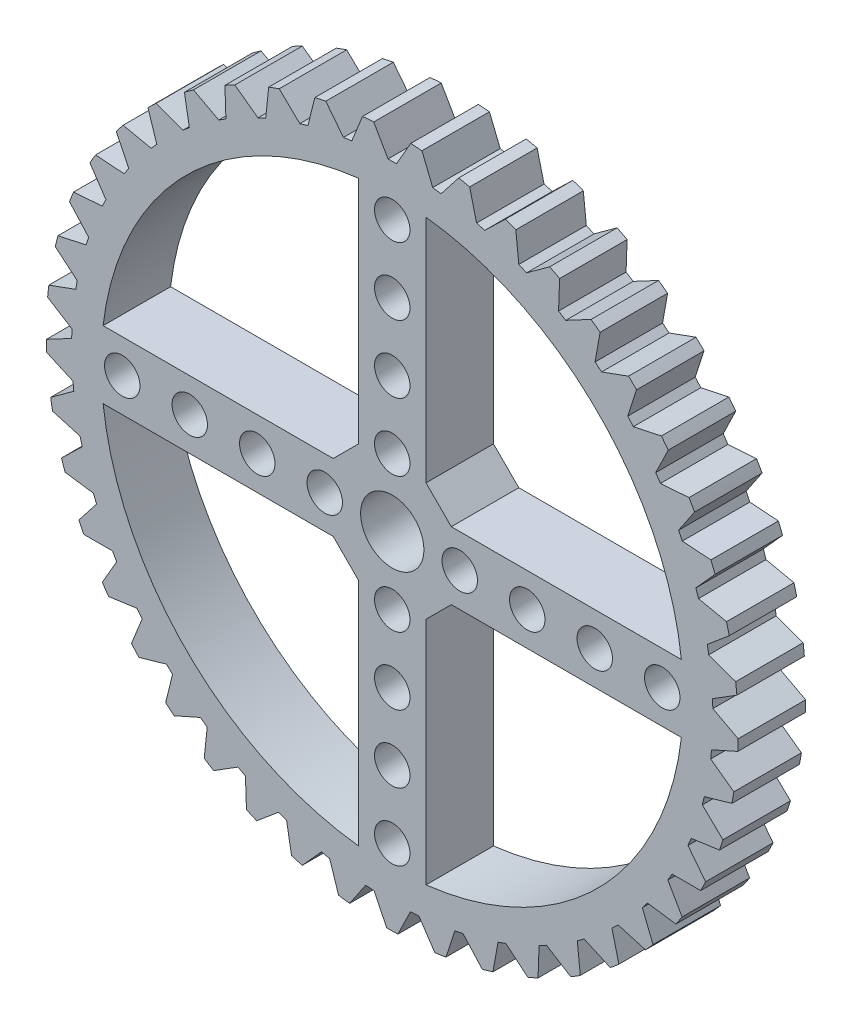
SolidWorks part; units mm, degrees
ref_plane "Front Plane" through (0, 0, 0) normal (0, 0, 1) x (1, 0, 0)
ref_plane "Top Plane" through (0, 0, 0) normal (0, 1, 0) x (1, 0, 0)
ref_plane "Right Plane" through (0, 0, 0) normal (1, 0, 0) x (0, 0, -1)
sketch "Sketch1" plane through (0, 0, 0) normal (0, 0, 1) x (1, 0, 0)
  line L0 (0, 41) -> (0, -41) construction
  line L1 (-41, 0) -> (41, 0) construction
  line L2 (-4, 34.2673) -> (-4, -34.2673)
  line L3 (4, 34.2673) -> (4, -34.2673)
  line L4 (-34.2673, 4) -> (34.2673, 4)
  line L5 (-34.2673, -4) -> (34.2673, -4)
  circle A0 centre (0, 0) radius 41
  circle A1 centre (0, 0) radius 34.5
  dimension "D1" = 82
  dimension "D2" = 6.5
  dimension "D3" = 4
  dimension "D4" = 4
  dimension "D5" = 4
  dimension "D6" = 4
extrude "Boss-Extrude1" add sketch "Sketch1" along normal blind 8 contours A0 A1 | L5 A1 L4 L3 | L2 A1 L3 L5 | L2 L5 L3 L4 | L4 A1 L5 L2 | L3 A1 L2 L4
chamfer "Chamfer1" distance 3 angle 45 4 edges at (-4, 4, 4) (4, 4, 4) (4, -4, 4) (-4, -4, 4)
sketch "Sketch2" plane through (0, 0, 8) normal (0, 0, 1) x (1, 0, 0)
  line L0 (-41, 0) -> (41, 0) construction
  circle A0 centre (0, 0) radius 3.75
  circle A1 centre (0, 0) radius 41 construction
  circle A2 centre (-8, 0) radius 2.1
  circle A4 centre (-16, 0) radius 2.1
  circle A5 centre (-24, 0) radius 2.1
  circle A6 centre (-32, 0) radius 2.1
  dimension "D1" = 7.5
  dimension "D2" = 4.2
  dimension "D3" = 8
  dimension "D4" = 8
  dimension "D5" = 8
  dimension "D6" = 8
extrude "Cut-Extrude1" cut sketch "Sketch2" against normal blind 10
sketch "Sketch3" plane through (0, 0, 8) normal (0, 0, 1) x (1, 0, 0)
  line L0 (-2.8094, 42) -> (-0.5, 38)
  line L1 (-0.5, 38) -> (0.5, 38)
  line L2 (0.5, 38) -> (2.8094, 42)
  line L3 (-2.8094, 42) -> (2.8094, 42)
  line L4 (0, 38) -> (0, 0) construction
  circle A1 centre (0, 0) radius 41 construction
  dimension "D5" = 38
  dimension "D1" = 120
  dimension "D2" = 120
  dimension "D3" = 4
  dimension "D4" = 1
extrude "Cut-Extrude4" cut sketch "Sketch3" against normal blind 10
pattern_circular "CirPattern1" count 45 over 360 about axis through (0, 0, 0) along (0, 0, 1) of "Cut-Extrude4"
pattern_circular "CirPattern2" count 4 over 360 about axis through (0, 0, 0) along (0, 0, 1) of "Cut-Extrude1"
